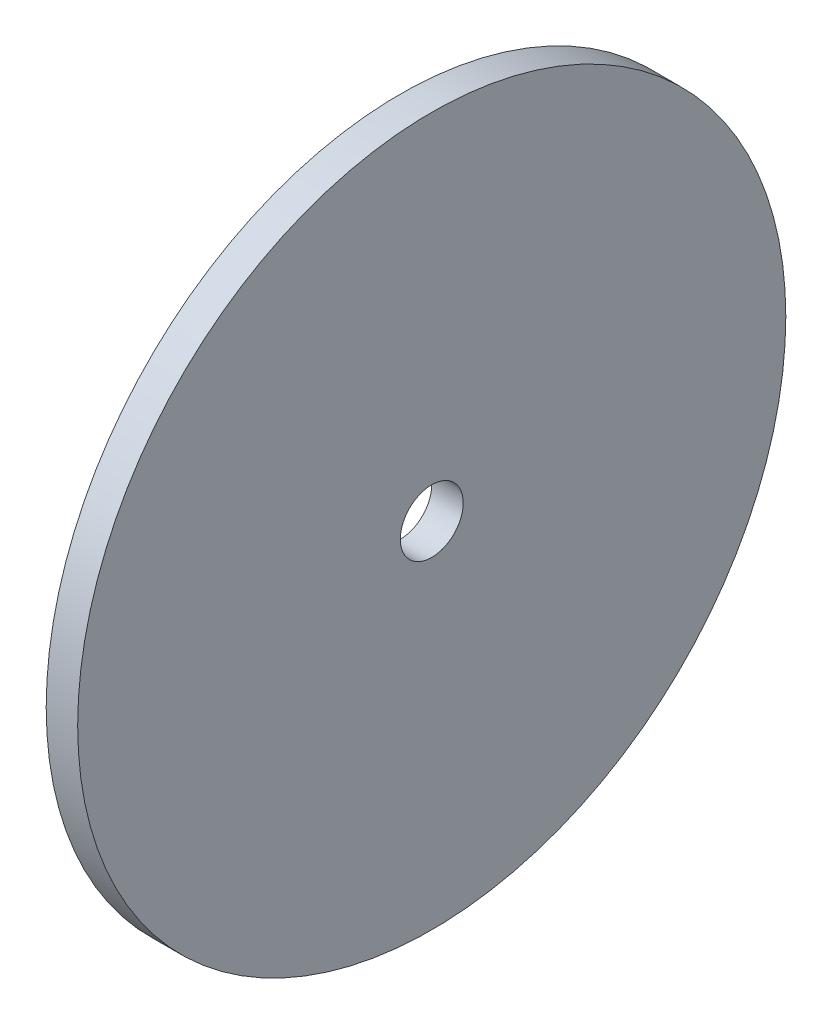
SolidWorks part; units mm, degrees
ref_plane "Front Plane" through (0, 0, 0) normal (0, 0, 1) x (1, 0, 0)
ref_plane "Top Plane" through (0, 0, 0) normal (0, 1, 0) x (1, 0, 0)
ref_plane "Right Plane" through (0, 0, 0) normal (1, 0, 0) x (0, 0, -1)
sketch "Sketch1" plane through (0, 0, 0) normal (1, 0, 0) x (0, 0, -1)
  circle A0 centre (0, 0) radius 45
  circle A1 centre (0, 0) radius 4
  dimension "D1" = 8
  dimension "D2" = 90
extrude "Boss-Extrude1" add sketch "Sketch1" along normal mid plane 4
